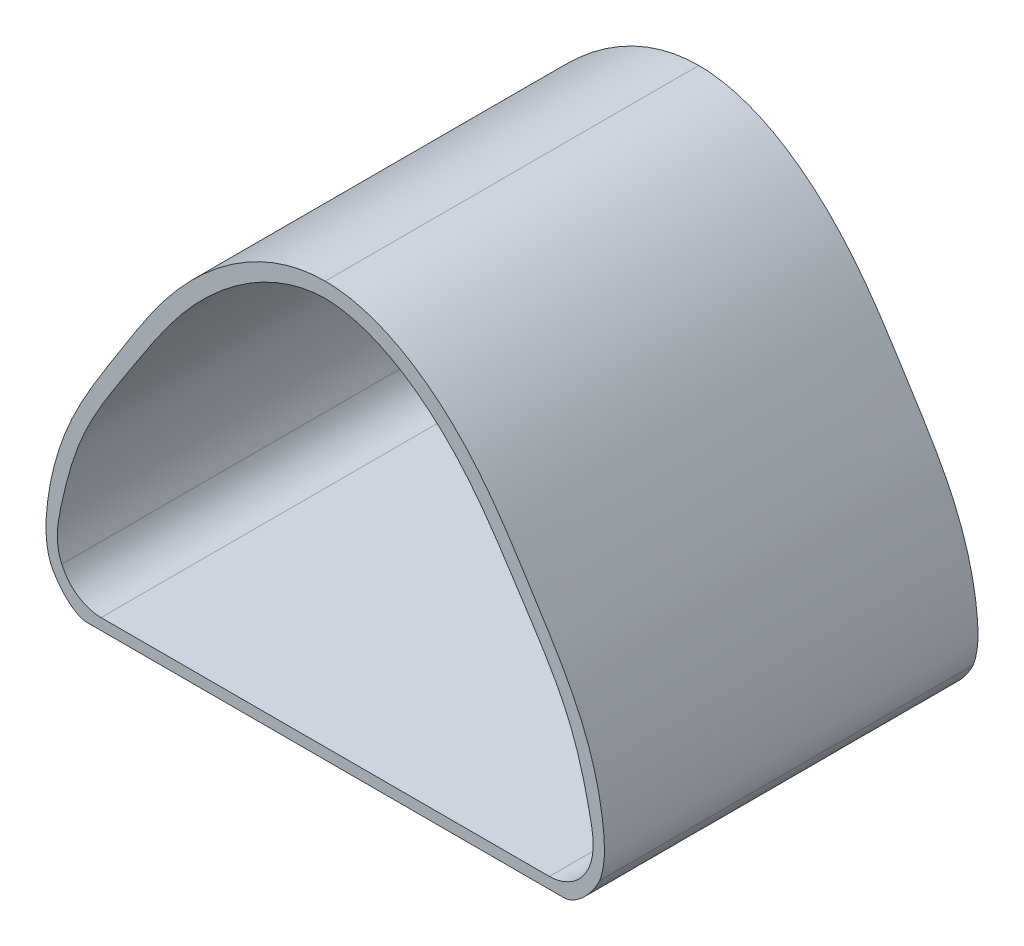
SolidWorks part; units mm, degrees
ref_plane "Front" through (0, 0, 0) normal (0, 0, 1) x (1, 0, 0)
ref_plane "Top" through (0, 0, 0) normal (0, 1, 0) x (1, 0, 0)
ref_plane "Right" through (0, 0, 0) normal (1, 0, 0) x (0, 0, -1)
sketch "草图1" plane through (0, 0, 0) normal (0, 0, 1) x (1, 0, 0)
  line L0 (0, 0) -> (0, -43.6365) construction
  line L1 (0, 0) -> (-54.6361, -25.4772) construction
  line L2 (0, 0) -> (57.9065, -27.0022) construction
  line L3 (-30, -20) -> (30, -20)
  line L4 (-32, -21.5) -> (32, -21.5)
  spline S0 degree 3 poles (-35.2584, -16.4413) (-34.9964, -17.0209) (-33.6906, -19.1426) (-31.1854, -20.0293) (-30, -20) knots 0 0 0 0 0.359901 1 1 1 1
  spline S1 degree 3 poles (-36.7339, -17.1293) (-36.4427, -17.7893) (-35.093, -20.0354) (-32.8599, -21.4831) (-32, -21.5) knots 0 0 0 0 0.489168 1 1 1 1
  spline S2 degree 3 poles (35.2584, -16.4413) (34.9964, -17.0209) (33.6906, -19.1426) (31.1854, -20.0293) (30, -20) knots 0 0 0 0 0.359901 1 1 1 1
  spline S3 degree 3 poles (36.7339, -17.1293) (36.4427, -17.7893) (35.093, -20.0354) (32.8599, -21.4831) (32, -21.5) knots 0 0 0 0 0.489168 1 1 1 1
  spline S4 degree 3 poles (0, 32) (-6.5255, 31.9036) (-17.5035, 24.3307) (-25.7176, 11.1374) (-32.7912, 0.6069) (-35.2636, -8.8645) (-36.2301, -14.212) (-35.2584, -16.4413) knots 0 0 0 0 0.310762 0.543528 0.745407 0.898184 1 1 1 1
  spline S5 degree 3 poles (0, 34) (-7.5559, 34.0116) (-18.9599, 25.9336) (-27.4108, 12.159) (-34.5056, 1.2316) (-37.3685, -8.7425) (-37.5155, -15.1167) (-36.7339, -17.1293) knots 0 0 0 0 0.330858 0.539323 0.730827 0.902655 1 1 1 1
  spline S6 degree 3 poles (0, 34) (7.5559, 34.0116) (18.9599, 25.9336) (27.4108, 12.159) (34.5056, 1.2316) (37.3685, -8.7425) (37.5155, -15.1167) (36.7339, -17.1293) knots 0 0 0 0 0.330858 0.539323 0.730827 0.902655 1 1 1 1
  spline S7 degree 3 poles (0, 32) (6.5255, 31.9036) (17.5035, 24.3307) (25.7176, 11.1374) (32.7912, 0.6069) (35.2636, -8.8645) (36.2301, -14.212) (35.2584, -16.4413) knots 0 0 0 0 0.310762 0.543528 0.745407 0.898184 1 1 1 1
  point P17 (0, 34)
  point P18 (0, 32)
  point P37 (34.3583, -18.8663)
  point P38 (32.0761, -18.2142)
  point P39 (34.0155, -15.8617)
  point P40 (31.2396, -14.5673)
  point P41 (-32.3649, -15.092)
  point P42 (36.0715, -16.8204)
  point P43 (38.5519, -19.7344)
  point P44 (0, 0)
  point P45 (38.2353, -17.8294)
  point P46 (36.8094, -18.8688)
  point P47 (36.7405, -17.1324)
  point P48 (-37.087, -9.1859)
  point P49 (-35.4795, -9.8749)
  point P50 (-39.2864, -18.3196)
  point P51 (-39.2264, -19.8295)
  point P52 (-39.7238, -18.5235)
  point P53 (-38.4388, -17.9243)
  point P54 (-37.6048, -19.5892)
  point P55 (-38, -9.8749)
  point P56 (-40.3611, -18.8207)
  point P57 (-39.5807, -20.3107)
  point P58 (36.5591, -19.2111)
  point P59 (36.8165, -17.1678)
  point P60 (35.7798, -18.8207)
  point P61 (38.5135, -17.9591)
  point P62 (37.241, -20)
  point P63 (35.1991, -16.4136)
  point P64 (34.2064, -18.4993)
  point P65 (37.0393, -17.2717)
  point P66 (35.7976, -19.6033)
  point P67 (34.535, -16.1039)
  point P68 (33.6245, -18.1515)
  point P69 (36.2048, -16.8826)
  point P70 (34.9147, -19.2301)
  point P71 (-37.0386, -9.6434)
  point P72 (-29.8408, -0.9984)
  point P73 (0, 0)
  point P74 (-24.6668, 9.9616)
  point P75 (-14.4429, 23.3584)
  point P76 (-35.3911, -9.9453)
  point P77 (-29.8408, 1.5403)
  point P78 (-23.1156, 11.6035)
  point P79 (-14.9448, 22.1831)
  point P80 (-17.1508, 21.8507)
  point P81 (-24.4543, 11.5103)
  point P82 (-32, 1.7501)
  point P83 (-36.7764, -10.4692)
  point P84 (-31.1574, 0)
  point P85 (-36.9299, -10.3577)
  point P86 (-34.685, -16.1739)
  point P87 (-23.9472, 9.3216)
  point P88 (-14.7035, 21.8507)
  point P89 (-24.7428, 11.6255)
  point P90 (-32.323, 1.6204)
  point P91 (-25.6405, 11.7277)
  point P92 (-17.9499, 22.8961)
  point P93 (-26.3627, 11.1909)
  point P94 (-33.0614, 1.0735)
  point P95 (-24.7919, 9.805)
  point P96 (-15.9133, 22.4364)
  point P97 (-31.3445, 0)
  point P98 (-19.6031, 23.3149)
  point P99 (-27.6987, 11.8108)
  point P100 (-34.1246, 0.5991)
  point P101 (-36.7339, -17.1293)
  point P102 (-34.9109, -19.7957)
  point P103 (-33.9011, -18.3881)
  point P104 (-35.2584, -16.4413)
  point P105 (-32, 0)
  point P106 (-26.0091, 10.4417)
  point P107 (-17.4481, 22.5748)
  point P108 (-37.2096, -10.5778)
  point P109 (-32.6211, -0.5977)
  point P110 (-26.1854, 10.5624)
  dimension "D3" = 65
  dimension "D4" = 32
  dimension "D5" = 20
  dimension "D6" = 60
  dimension "D7" = 34
  dimension "D8" = 1.5
  dimension "D9" = 64
extrude "凸台-拉伸1" add sketch "草图1" along normal blind 50
